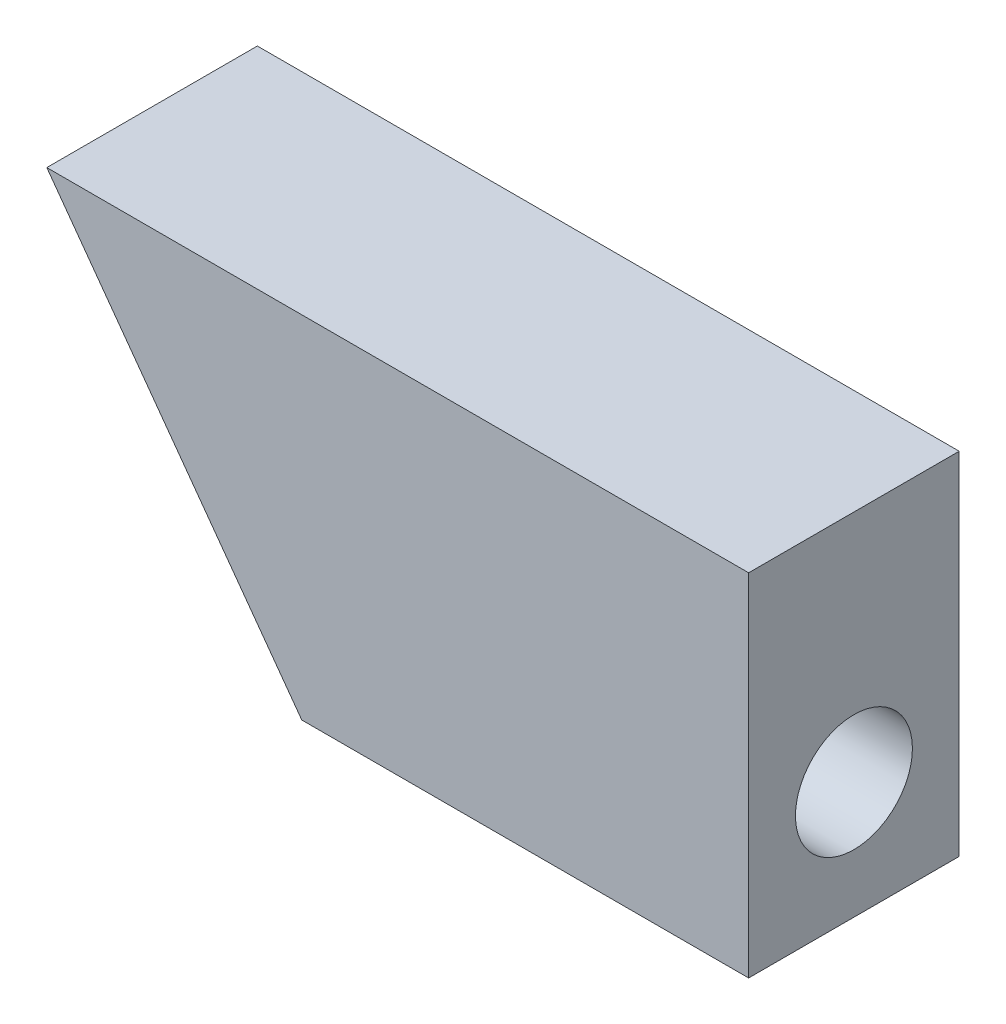
SolidWorks part; units mm, degrees
material "ABS"
ref_plane "前视基准面" through (0, 0, 0) normal (0, 0, 1) x (1, 0, 0)
ref_plane "上视基准面" through (0, 0, 0) normal (0, 1, 0) x (1, 0, 0)
ref_plane "右视基准面" through (0, 0, 0) normal (1, 0, 0) x (0, 0, -1)
other "Configuration Table"
sketch "草图1" plane through (0, 0, 0) normal (0, 0, 1) x (1, 0, 0)
  line L0 (19.1019, 0) -> (0, 0)
  line L5 (0, 0) -> (-10.8981, 15)
  line L6 (-10.8981, 15) -> (19.1019, 15)
  line L7 (19.1019, 15) -> (19.1019, 0)
  dimension "D1" = 15
  dimension "D2" = 36
  dimension "D3" = 30
extrude "凸台-拉伸1" add sketch "草图1" along normal blind 9
sketch "草图2" plane through (19.1019, 0, 0) normal (1, 0, 0) x (0, 0, -1)
  line L0 (-4.5, 0) -> (-4.5, 15) construction
  line L1 (-9, 0) -> (0, 0) construction
  line L2 (-9, 15) -> (0, 15) construction
  circle A0 centre (-4.5, 5) radius 2.5
  dimension "D1" = 5
  dimension "D2" = 5
extrude "切除-拉伸1" cut sketch "草图2" against normal blind 30
